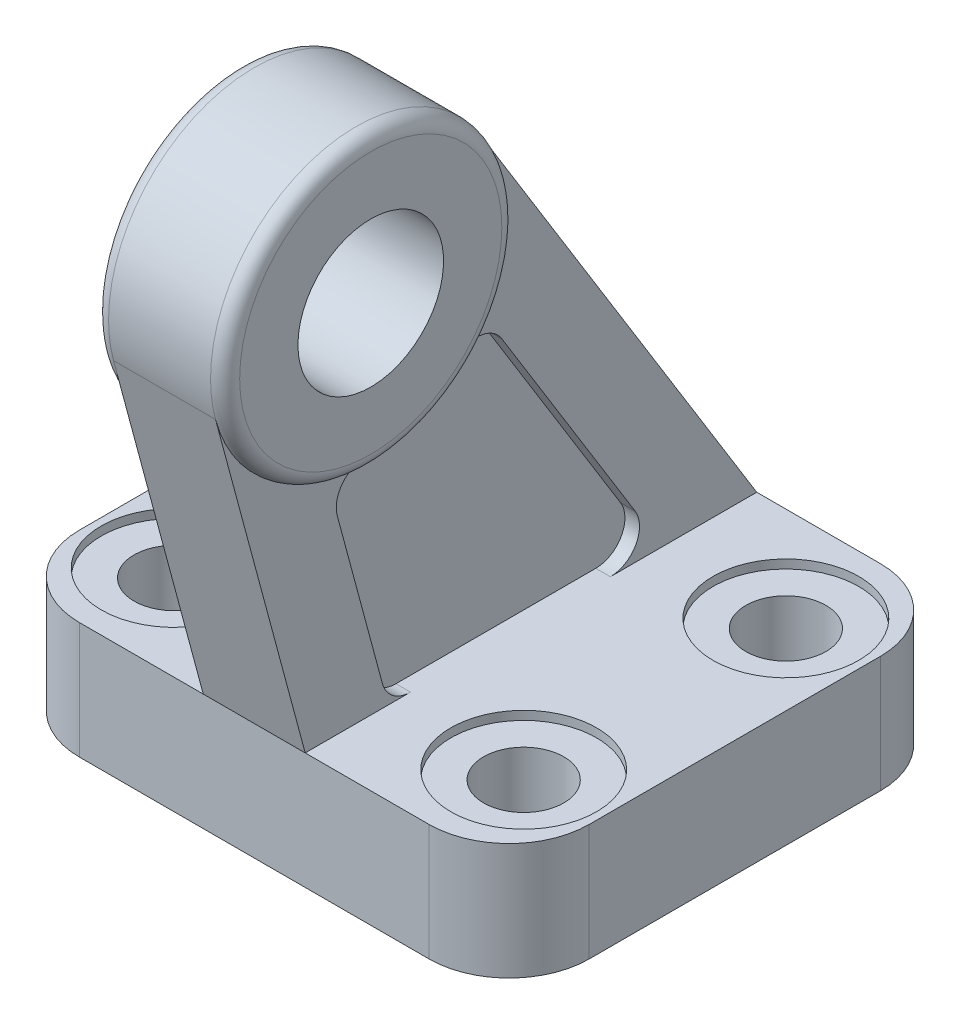
SolidWorks part; units mm, degrees
ref_plane "Front Plane" through (0, 0, 0) normal (0, 0, 1) x (1, 0, 0)
ref_plane "Top Plane" through (0, 0, 0) normal (0, 1, 0) x (1, 0, 0)
ref_plane "Right Plane" through (0, 0, 0) normal (1, 0, 0) x (0, 0, -1)
ref_plane "Plane1" through (0, 0, 0) normal (0, 1, 0) x (1, 0, 0)
sketch "Sketch1" plane through (0, 0, 0) normal (0, 1, 0) x (1, 0, 0)
  line L0 (-12, -15.5) -> (12, -15.5)
  line L1 (17.5, -10) -> (17.5, 10)
  line L2 (12, 15.5) -> (-12, 15.5)
  line L3 (-17.5, 10) -> (-17.5, -10)
  arc A0 (-17.5, -10) -> (-12, -15.5) centre (-12, -10) ccw
  arc A1 (12, -15.5) -> (17.5, -10) centre (12, -10) ccw
  arc A2 (17.5, 10) -> (12, 15.5) centre (12, 10) ccw
  arc A3 (-12, 15.5) -> (-17.5, 10) centre (-12, 10) ccw
  circle A4 centre (12, 9) radius 2.75
  circle A5 centre (12, -9) radius 2.75
  circle A6 centre (-12, 9) radius 2.75
  circle A7 centre (-12, -9) radius 2.75
extrude "Boss-Extrude1" add sketch "Sketch1" along normal blind 8
ref_plane "Plane2" through (0, 0, 0) normal (1, 0, 0) x (0, 0, -1)
sketch "Sketch2" plane through (0, 0, 0) normal (1, 0, 0) x (0, 0, -1)
  line L0 (-21.6571, 30.9039) -> (-15.5, 8)
  line L1 (-15.5, 8) -> (15.5, 8)
  line L2 (15.5, 8) -> (-3.4916, 38.7542)
  arc A0 (-3.4916, 38.7542) -> (-21.6571, 30.9039) centre (-12, 33.5) cw
extrude "Boss-Extrude2" add sketch "Sketch2" against normal blind 3.5 and the other way blind 3.5
ref_plane "Plane3" through (3.5, 0, 0) normal (1, 0, 0) x (0, 0, -1)
sketch "Sketch3" plane through (3.5, 0, 0) normal (1, 0, 0) x (0, 0, -1)
  line L0 (-13.2988, 20.9975) -> (-10.2028, 9.4808)
  line L1 (-8.2714, 8) -> (5.4502, 8)
  line L2 (7.1518, 11.0508) -> (-2.0045, 25.8783)
  arc A0 (-11.4728, 23.5139) -> (-13.2988, 20.9975) centre (-11.3673, 21.5167) ccw
  arc A1 (-10.2028, 9.4808) -> (-8.2714, 8) centre (-8.2714, 10) ccw
  arc A2 (5.4502, 8) -> (7.1518, 11.0508) centre (5.4502, 10) ccw
  arc A3 (-2.0045, 25.8783) -> (-5.0885, 26.2729) centre (-3.7062, 24.8275) ccw
  arc A4 (-5.0885, 26.2729) -> (-11.4728, 23.5139) centre (-12, 33.5) cw
extrude "Cut-Extrude1" cut sketch "Sketch3" against normal blind 1
ref_plane "Plane4" through (-3.5, 0, 0) normal (1, 0, 0) x (0, 0, -1)
sketch "Sketch4" plane through (-3.5, 0, 0) normal (1, 0, 0) x (0, 0, -1)
  line L0 (-13.2988, 20.9975) -> (-10.2028, 9.4808)
  line L1 (-8.2714, 8) -> (5.4502, 8)
  line L2 (7.1518, 11.0508) -> (-2.0045, 25.8783)
  arc A0 (-11.4728, 23.5139) -> (-13.2988, 20.9975) centre (-11.3673, 21.5167) ccw
  arc A1 (-10.2028, 9.4808) -> (-8.2714, 8) centre (-8.2714, 10) ccw
  arc A2 (5.4502, 8) -> (7.1518, 11.0508) centre (5.4502, 10) ccw
  arc A3 (-2.0045, 25.8783) -> (-5.0885, 26.2729) centre (-3.7062, 24.8275) ccw
  arc A4 (-5.0885, 26.2729) -> (-11.4728, 23.5139) centre (-12, 33.5) cw
extrude "Cut-Extrude2" cut sketch "Sketch4" along normal blind 1
ref_plane "Plane5" through (0, 0, 12) normal (0, 0, 1) x (1, 0, 0)
sketch "Sketch5" plane through (0, 0, 12) normal (0, 0, 1) x (1, 0, 0)
  line L0 (-4.5, 42.5) -> (-4.5, 38.5)
  line L1 (-4.5, 38.5) -> (4.5, 38.5)
  line L2 (4.5, 38.5) -> (4.5, 42.5)
  line L3 (3.5, 43.5) -> (-3.5, 43.5)
  line L4 (4.5, 33.5) -> (-4.5, 33.5) construction
  arc A0 (4.5, 42.5) -> (3.5, 43.5) centre (3.5, 42.5) ccw
  arc A1 (-3.5, 43.5) -> (-4.5, 42.5) centre (-3.5, 42.5) ccw
revolve "Revolve1" add sketch "Sketch5" angle 360 about L4
ref_plane "Plane6" through (0, 0, 0) normal (0, 1, 0) x (1, 0, 0)
sketch "Sketch6" plane through (0, 0, 0) normal (0, 1, 0) x (1, 0, 0)
  line L0 (-12, 1.7716) -> (-12, -1.7716)
  line L1 (-4.567, -10) -> (4.567, -10)
  line L2 (12, -1.7716) -> (12, 1.7716)
  line L3 (4.567, 10) -> (-4.567, 10)
  arc A0 (-12, -1.7716) -> (-10.5333, -3.6992) centre (-10, -1.7716) ccw
  arc A1 (-10.5333, -3.6992) -> (-6.5491, -8.2667) centre (-12, -9) cw
  arc A2 (-6.5491, -8.2667) -> (-4.567, -10) centre (-4.567, -8) ccw
  arc A3 (4.567, -10) -> (6.5491, -8.2667) centre (4.567, -8) ccw
  arc A4 (6.5491, -8.2667) -> (10.5333, -3.6992) centre (12, -9) cw
  arc A5 (10.5333, -3.6992) -> (12, -1.7716) centre (10, -1.7716) ccw
  arc A6 (12, 1.7716) -> (10.5333, 3.6992) centre (10, 1.7716) ccw
  arc A7 (10.5333, 3.6992) -> (6.5491, 8.2667) centre (12, 9) cw
  arc A8 (6.5491, 8.2667) -> (4.567, 10) centre (4.567, 8) ccw
  arc A9 (-4.567, 10) -> (-6.5491, 8.2667) centre (-4.567, 8) ccw
  arc A10 (-6.5491, 8.2667) -> (-10.5333, 3.6992) centre (-12, 9) cw
  arc A11 (-10.5333, 3.6992) -> (-12, 1.7716) centre (-10, 1.7716) ccw
extrude "Cut-Extrude3" cut sketch "Sketch6" along normal blind 4
ref_plane "Plane7" through (0, 8, 0) normal (0, 1, 0) x (1, 0, 0)
sketch "Sketch7" plane through (0, 8, 0) normal (0, 1, 0) x (1, 0, 0)
  circle A0 centre (12, 9) radius 5
extrude "Cut-Extrude4" cut sketch "Sketch7" against normal blind 0.6
ref_plane "Plane8" through (0, 8, 0) normal (0, 1, 0) x (1, 0, 0)
sketch "Sketch8" plane through (0, 8, 0) normal (0, 1, 0) x (1, 0, 0)
  circle A0 centre (-12, 9) radius 5
extrude "Cut-Extrude5" cut sketch "Sketch8" against normal blind 0.6
ref_plane "Plane9" through (0, 8, 0) normal (0, 1, 0) x (1, 0, 0)
sketch "Sketch9" plane through (0, 8, 0) normal (0, 1, 0) x (1, 0, 0)
  circle A0 centre (12, -9) radius 5
extrude "Cut-Extrude6" cut sketch "Sketch9" against normal blind 0.6
ref_plane "Plane10" through (0, 8, 0) normal (0, 1, 0) x (1, 0, 0)
sketch "Sketch10" plane through (0, 8, 0) normal (0, 1, 0) x (1, 0, 0)
  circle A0 centre (-12, -9) radius 5
extrude "Cut-Extrude7" cut sketch "Sketch10" against normal blind 0.6
